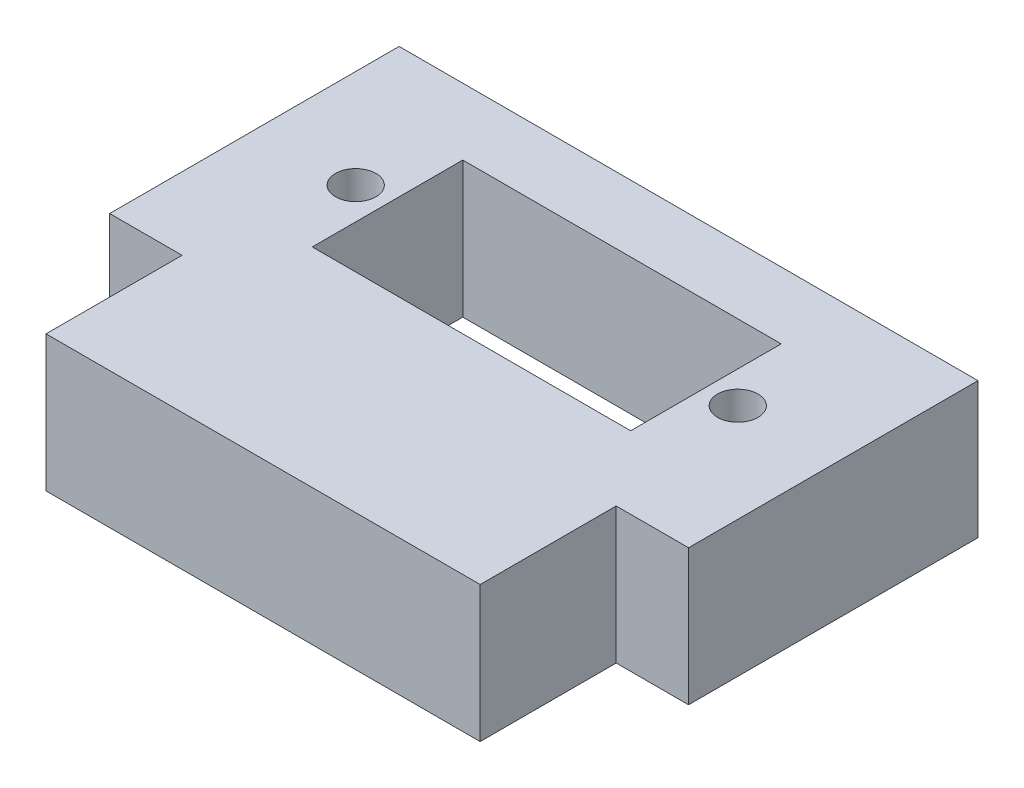
SolidWorks part; units mm, degrees
ref_plane "Front" through (0, 0, 0) normal (0, 0, 1) x (1, 0, 0)
ref_plane "Top" through (0, 0, 0) normal (0, 1, 0) x (1, 0, 0)
ref_plane "Right" through (0, 0, 0) normal (1, 0, 0) x (0, 0, -1)
sketch "Tilt Mount Sketch" plane through (0, 0, 0) normal (0, 1, 0) x (1, 0, 0)
  line L0 (44.45, 0) -> (50.8, 0)
  line L1 (0, 0) -> (6.35, 0)
  line L2 (0, 0) -> (0, 25.4)
  line L3 (0, 25.4) -> (50.8, 25.4)
  line L4 (50.8, 0) -> (50.8, 25.4)
  line L6 (6.35, 0) -> (6.35, -11.938)
  line L7 (6.35, -11.938) -> (44.45, -11.938)
  line L8 (44.45, 0) -> (44.45, -11.938)
  dimension "D1" = 50.8
  dimension "D2" = 38.1
  dimension "D3" = 11.938
  dimension "D4" = 25.4
extrude "Tilt Mount" add sketch "Tilt Mount Sketch" along normal blind 11.938
sketch "Servo Hole Sketch" plane through (0, 11.938, 0) normal (0, 1, 0) x (1, 0, 0)
  line L0 (0, 0) -> (50.8, 0) construction
  line L1 (39.37, 6.35) -> (11.43, 6.35)
  line L2 (39.37, 6.35) -> (39.37, 19.558)
  line L3 (39.37, 19.558) -> (11.43, 19.558)
  line L4 (11.43, 6.35) -> (11.43, 19.558)
  line L5 (11.43, 19.558) -> (0, 19.558) construction
  line L6 (0, 25.4) -> (0, 0) construction
  line L7 (39.37, 19.558) -> (50.8, 19.558) construction
  line L8 (50.8, 0) -> (50.8, 25.4) construction
  dimension "D1" = 27.94
  dimension "D2" = 13.208
  dimension "D3" = 6.35
sketch "Mounting Holes Guide Sketch" plane through (0, 11.938, 0) normal (0, 1, 0) x (1, 0, 0)
  line L0 (11.43, 19.558) -> (0, 19.558) construction
  line L2 (5.207, 19.558) -> (5.207, 6.35) construction
  line L3 (5.207, 6.35) -> (45.593, 6.35) construction
  line L4 (45.593, 19.558) -> (45.593, 6.35) construction
  line L5 (11.43, 19.558) -> (5.207, 19.558) construction
  line L6 (39.37, 19.558) -> (45.593, 19.558) construction
  line L7 (5.207, 12.954) -> (45.593, 12.954) construction
  line L8 (25.4, 19.558) -> (25.4, 6.35) construction
  line L9 (39.37, 19.558) -> (11.43, 19.558) construction
  line L10 (11.43, 6.35) -> (11.43, 19.558) construction
  circle A0 centre (8.636, 12.954) radius 1.778
  circle A1 centre (42.164, 12.954) radius 1.778
  dimension "D2" = 3.556
  dimension "D3" = 2.794
  dimension "D1" = 40.386
extrude "Servo Hole" cut sketch "Servo Hole Sketch" against normal through all
extrude "Mounting Holes" cut sketch "Mounting Holes Guide Sketch" against normal through all
